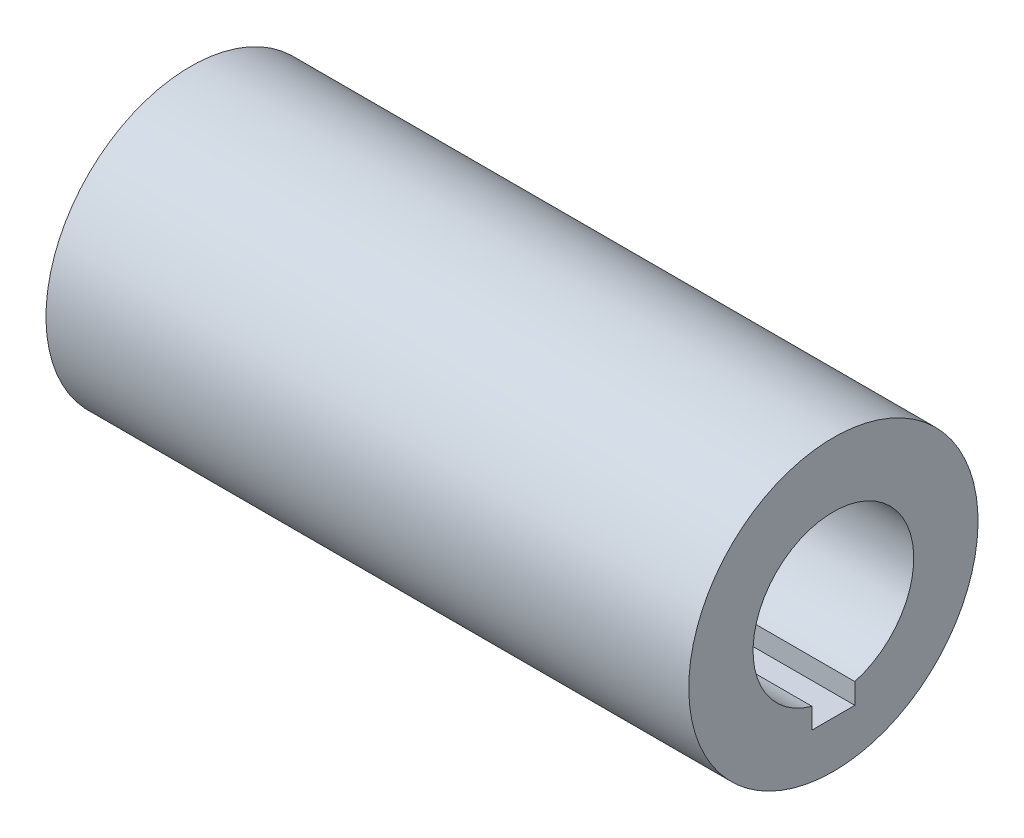
SolidWorks part; units mm, degrees
ref_plane "Front Plane" through (0, 0, 0) normal (0, 0, 1) x (1, 0, 0)
ref_plane "Top Plane" through (0, 0, 0) normal (0, 1, 0) x (1, 0, 0)
ref_plane "Right Plane" through (0, 0, 0) normal (1, 0, 0) x (0, 0, -1)
sketch "Çizim1" plane through (0, 0, 0) normal (0, 0, 1) x (1, 0, 0)
  line L0 (-60, 0) -> (60, 0) construction
  line L2 (-60, 15) -> (60, 15)
  line L3 (-60, 15) -> (-60, 27)
  line L4 (-60, 27) -> (60, 27)
  line L5 (60, 15) -> (60, 27)
  point P3 (0, 0)
  point P8 (0, 0)
  dimension "D1" = 120
  dimension "D2" = 12
  dimension "D3" = 15
  dimension "D4" = 120
revolve "Döndür1" add sketch "Çizim1" angle 360 about L0
sketch "Çizim2" plane through (0, 0, 0) normal (0, 1, 0) x (1, 0, 0)
  line L0 (-60, 27) -> (-60, -27) construction
  line L1 (-60, 4) -> (60, 4)
  line L2 (-60, 4) -> (-60, -4)
  line L3 (-60, -4) -> (60, -4)
  line L4 (60, 4) -> (60, -4)
  line L5 (60, -27) -> (60, 27) construction
  point P8 (60, 0)
  dimension "D1" = 8
extrude "Kes-Ekstrüzyon1" cut sketch "Çizim2" against normal blind 18.3
